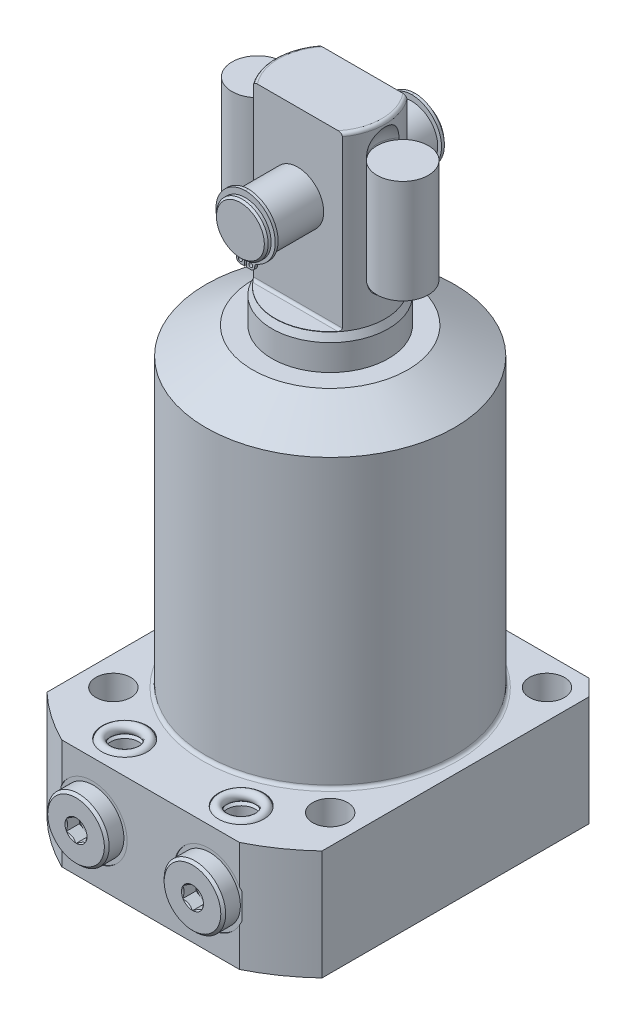
SolidWorks part; units mm, degrees
material "AISI 1020"
ref_plane "Front Plane" through (0, 0, 0) normal (0, 0, 1) x (1, 0, 0)
ref_plane "Top Plane" through (0, 0, 0) normal (0, 1, 0) x (1, 0, 0)
ref_plane "Right Plane" through (0, 0, 0) normal (1, 0, 0) x (0, 0, -1)
sketch "Sketch1" plane through (0, 0, 0) normal (0, 0, 1) x (1, 0, 0)
  line L0 (18, 0) -> (18, 105)
  line L1 (18, 105) -> (17, 107.1445)
  line L2 (17, 107.1445) -> (17, 159.25)
  line L3 (16, 160.25) -> (0, 160.25)
  line L4 (0, 61.9815) -> (0, 93.5758) construction
  line L8 (0, -3.075) -> (0, 64.575) construction
  line L9 (18, 0) -> (0, 0)
  line L10 (0, 0) -> (0, 160.25)
  line L11 (-25.0821, -34) -> (21.8096, -34) construction
  arc A0 (17, 159.25) -> (16, 160.25) centre (16, 159.25) ccw
  dimension "D1" = 1
  dimension "D2" = 36
  dimension "D3" = 34
  dimension "D4" = 55.25
  dimension "D5" = 34
  dimension "D6" = 25
  dimension "D7" = 194.25
revolve "PLUNGER" add sketch "Sketch1" angle 360 about L8
ref_plane "FLAT_SKTCH_PLN" through (0, 0, 0) normal (1, 0, 0) x (0, 0, -1)
sketch "Sketch17" plane through (0, 0, 0) normal (1, 0, 0) x (0, 0, -1)
  line L0 (16, 160.25) -> (-16, 160.25) construction
  line L1 (17, 107.1445) -> (17, 159.25) construction
  line L2 (16, 160.25) -> (-16, 160.25)
  line L3 (17, 107.1445) -> (17, 159.25)
  line L5 (10, 160.25) -> (17, 160.25)
  line L6 (10, 160.25) -> (10, 108.05)
  line L7 (10.8, 107.25) -> (17, 107.25)
  line L8 (17, 160.25) -> (17, 107.25)
  line L9 (0, 159.25) -> (0, 107.1445) construction
  line L10 (0, 57.0947) -> (0, 92.2162) construction
  line L11 (0, 105) -> (0, 0) construction
  line L12 (0, 105) -> (0, 107.1445) construction
  line L13 (-17, 160.25) -> (-17, 107.25)
  line L14 (-10.8, 107.25) -> (-17, 107.25)
  line L15 (-10, 160.25) -> (-10, 108.05)
  line L16 (-10, 160.25) -> (-17, 160.25)
  line L17 (-17, 107.1445) -> (-17, 159.25)
  arc A0 (10, 108.05) -> (10.8, 107.25) centre (10.8, 108.05) ccw
  arc A1 (-10, 108.05) -> (-10.8, 107.25) centre (-10.8, 108.05) cw
  dimension "D3" = 0.8
  dimension "D1" = 53
  dimension "D2" = 20
extrude "FLATS" cut sketch "Sketch17" against normal mid plane 100 contours L6 A0 L7 L8 L5 | L13 L14 A1 L15 L16
sketch "Sketch22" plane through (0, 0, 0) normal (1, 0, 0) x (0, 0, -1)
  line L0 (-11.5689, 136.25) -> (12.3381, 136.25) construction
  line L1 (0, 87.9433) -> (0, 65.5754) construction
  line L2 (0, 163.8601) -> (0, 151.5297) construction
  line L3 (0, 159.25) -> (0, 107.1445) construction
  line L4 (10, 160.25) -> (-10, 160.25) construction
  line L5 (10, 160.25) -> (-10, 160.25)
  line L6 (27.75, 143.65) -> (27.15, 144.25)
  line L7 (27.15, 144.25) -> (26.25, 144.25)
  line L8 (27.75, 143.65) -> (27.75, 136.25)
  line L9 (27.75, 136.25) -> (-27.75, 136.25)
  line L11 (26.25, 144.25) -> (26.25, 143.7175)
  line L12 (26.25, 143.7175) -> (25.25, 143.7175)
  line L13 (25.25, 143.7175) -> (25.25, 144.25)
  line L14 (25.25, 144.25) -> (-25.25, 144.25)
  line L15 (-25.25, 143.7175) -> (-25.25, 144.25)
  line L16 (-26.25, 143.7175) -> (-25.25, 143.7175)
  line L17 (-26.25, 144.25) -> (-26.25, 143.7175)
  line L18 (-27.75, 143.65) -> (-27.75, 136.25)
  line L19 (-27.15, 144.25) -> (-26.25, 144.25)
  line L20 (-27.75, 143.65) -> (-27.15, 144.25)
  dimension "D1" = 24
  dimension "D2" = 45
  dimension "D3" = 0.6
  dimension "D4" = 16
  dimension "D5" = 1
  dimension "D6" = 14.935
  dimension "D7" = 55.5
  dimension "D8" = 50.5
revolve "PIVOT_PIN" add sketch "Sketch22" angle 360 about L0
sketch "Sketch23" plane through (0, 0, -25.25) normal (0, 0, -1) x (-1, 0, 0)
  line L0 (0, 79.466) -> (0, 70.8639) construction
  line L1 (0, 159.25) -> (0, 107.1445) construction
  line L2 (0, 136.25) -> (-4.1358, 126.8979) construction
  line L3 (-0.35, 125.7079) -> (-1.61, 125.7079)
  line L4 (0, 136.25) -> (4.1358, 126.8979) construction
  line L5 (0.35, 128.5079) -> (0.35, 125.7079)
  line L6 (-0.35, 128.5079) -> (-0.35, 125.7079)
  line L7 (0.35, 125.7079) -> (1.61, 125.7079)
  arc A0 (0.35, 128.5079) -> (-0.35, 128.5079) centre (0, 136.25) ccw
  arc A1 (-2.8, 126.8979) -> (-1.61, 125.7079) centre (-1.61, 126.8979) ccw
  arc A2 (-2.8, 126.8979) -> (-3.5955, 128.1195) centre (-4.1358, 126.8979) ccw
  arc A3 (-3.5955, 128.1195) -> (0, 146.03) centre (0.1884, 136.676) cw
  circle A4 centre (-1.61, 126.8979) radius 0.595
  circle A5 centre (1.61, 126.8979) radius 0.595
  arc A6 (3.5955, 128.1195) -> (0, 146.03) centre (-0.1884, 136.676) ccw
  arc A7 (2.8, 126.8979) -> (3.5955, 128.1195) centre (4.1358, 126.8979) cw
  arc A8 (2.8, 126.8979) -> (1.61, 125.7079) centre (1.61, 126.8979) cw
  point P17 (-3.1344, 129.1621)
  point P27 (3.1344, 129.1621)
  point P28 (0, 144)
  dimension "D1" = 15.5
  dimension "D3" = 1.19
  dimension "D8" = 1.19
  dimension "D2" = 0.7
  dimension "D4" = 2.8
  dimension "D5" = 2.8
  dimension "D6" = 2.03
  dimension "D7" = 1.14
extrude "RETAINING_RING" add sketch "Sketch23" along normal blind 0.89
ref_plane "PIN_CL" through (0, 0, 0) normal (0, 0, 1) x (1, 0, 0)
mirror "RETAINING_RING-OPP" about plane through (0, 0, 0) normal (0, 0, 1) of "RETAINING_RING"
sketch "Sketch20" plane through (0, 0, 0) normal (0, 0, 1) x (1, 0, 0)
  line L0 (-12.49, 160.25) -> (12.49, 160.25) construction
  line L1 (-12.49, 160.25) -> (12.49, 160.25)
  line L2 (0, 87.5232) -> (0, 65.9324) construction
  line L3 (0, 163.858) -> (0, 151.534) construction
  line L4 (0, 159.25) -> (0, 107.1445) construction
  line L5 (22.4375, 82.048) -> (22.4375, 54.8595) construction
  line L6 (14.5, 152.75) -> (14.5, 119.75)
  line L7 (22.4375, 160.6875) -> (22.4375, 111.8125)
  arc A0 (22.4375, 160.6875) -> (14.5, 152.75) centre (22.4375, 152.75) ccw
  arc A1 (14.5, 119.75) -> (22.4375, 111.8125) centre (22.4375, 119.75) ccw
  dimension "D3" = 33
  dimension "D1" = 14.5
  dimension "D2" = 15.875
  dimension "D4" = 7.5
revolve "SPRING_SLOT" cut sketch "Sketch20" angle 360 about L5
mirror "SPRING_SLOT_OPP" about plane through (0, 0, 0) normal (1, 0, 0) of "SPRING_SLOT"
sketch "Sketch24" plane through (0, 0, 0) normal (0, 0, 1) x (1, 0, 0)
  line L0 (7.2759, 136.25) -> (-10.8708, 136.25) construction
  line L1 (-22.4075, 84.5678) -> (-22.4075, 68.6953) construction
  line L2 (-14.5, 119.75) -> (-14.5, 152.75) construction
  line L3 (-14.47, 152.25) -> (-22.4075, 152.25)
  line L4 (-14.47, 152.25) -> (-14.47, 120.25)
  line L6 (-22.4075, 152.25) -> (-22.4075, 120.25)
  line L7 (-14.47, 120.25) -> (-22.4075, 120.25)
  dimension "D1" = 15.875
  dimension "D2" = 32
  dimension "D3" = 0.03
revolve "SPRING" add sketch "Sketch24" angle 360 about L1
mirror "SPRING_OPP" about plane through (0, 0, 0) normal (1, 0, 0) of "SPRING"
sketch "Sketch6" plane through (0, 0, 0) normal (0, 0, 1) x (1, 0, 0)
  line L0 (0, -34) -> (0, 67.6291) construction
  line L1 (0, 97) -> (24, 97)
  line L2 (24, 97) -> (38.385, 88.6948)
  line L3 (61.915, 0) -> (61.915, -34)
  line L4 (0, -34) -> (61.915, -34)
  line L5 (38.385, 0) -> (38.385, 88.6948)
  line L6 (61.915, 0) -> (38.385, 0)
  line L7 (0, -34) -> (0, 97)
  dimension "D1" = 76.77
  dimension "D2" = 34
  dimension "D3" = 131
  dimension "D4" = 123.83
  dimension "D5" = 30
  dimension "D6" = 48
revolve "BODY_REVOLVE" add sketch "Sketch6" angle 360 about L0
sketch "Sketch7" plane through (0, 0, 0) normal (0, 1, 0) x (-1, 0, 0)
  line L0 (0, 0) -> (0, -52.3237) construction
  line L1 (-42.5, 55.5) -> (42.5, 55.5)
  line L2 (-42.5, 55.5) -> (-42.5, -42.5)
  line L3 (-42.5, -42.5) -> (42.5, -42.5)
  line L4 (42.5, 55.5) -> (42.5, -42.5)
  dimension "D1" = 85
  dimension "D2" = 98
  dimension "D3" = 42.5
extrude "FLANGE_SIDES" cut sketch "Sketch7" against normal through all flip side to cut
sketch "Sketch8" plane through (0, -34, 0) normal (0, -1, 0) x (1, 0, 0)
  circle A0 centre (-33.5, 33.5) radius 5.4
  dimension "D1" = 10.8
  dimension "D2" = 33.5
  dimension "D3" = 33.5
extrude "MOUNTING HOLES" cut sketch "Sketch8" against normal through all
pattern_circular "MOUNTING_PATTERN" count 4 over 360 about axis through (0, 0, 0) along (0, 1, 0) of "MOUNTING HOLES"
chamfer "FLANGE_CHAMFER" distance 5 angle 45 2 edges at (-42.5, -17, -42.5) (42.5, -17, -42.5)
fillet "BODY_FILLET" radius 1 1 edges at (38.385, 0, 0)
ref_plane "FLANGE-PORT_PLANE" through (0, -17, 0) normal (0, -1, 0) x (1, 0, 0)
sketch "Sketch11" plane through (0, -17, 0) normal (0, -1, 0) x (1, 0, 0)
  line L0 (-18, 42.9716) -> (-18, 19.7499) construction
  line L1 (-28.75, 55.5) -> (-28.75, 55.25)
  line L3 (-28.75, 55.25) -> (-24.65, 55.25)
  line L4 (-24.65, 55.25) -> (-23.945, 54.545)
  line L5 (-23.945, 54.545) -> (-23.945, 36.53)
  line L6 (-23.945, 36.53) -> (-18, 36.53)
  line L7 (-18, 36.53) -> (-18, 55.5)
  line L8 (-18, 55.5) -> (-28.75, 55.5)
  line L10 (27.4448, 55.5) -> (-27.4448, 55.5) construction
  dimension "D1" = 18
  dimension "D2" = 0.25
  dimension "D3" = 11.89
  dimension "D4" = 18.72
  dimension "D5" = 21.5
  dimension "D6" = 45
  dimension "D7" = 0.705
revolve "PORT SPOT FACE" cut sketch "Sketch11" angle 360 about L0
ref_plane "MANIFOLD_PORT_PLANE" through (0, 0, 45.5) normal (0, 0, 1) x (1, 0, 0)
sketch "Sketch13" plane through (0, 0, 45.5) normal (0, 0, 1) x (1, 0, 0)
  line L0 (-22.375, -22) -> (-22.375, -31)
  line L1 (-22.375, -31) -> (-23.125, -31.75)
  line L2 (-23.125, -31.75) -> (-25, -31.75)
  line L3 (-25, -31.75) -> (-25, -34)
  line L5 (-25, -34) -> (-18, -34)
  line L6 (-18, -34) -> (-18, -22)
  line L7 (-18, -22) -> (-22.375, -22)
  line L8 (-18, 15.2099) -> (-18, -4.3918) construction
  line L10 (27.4448, -34) -> (-27.4448, -34) construction
  dimension "D1" = 18
  dimension "D2" = 8.75
  dimension "D3" = 12
  dimension "D4" = 2.25
  dimension "D5" = 14
  dimension "D6" = 45
  dimension "D7" = 0.75
revolve "BOTTOM_MANIFOLD_PORT" cut sketch "Sketch13" angle 360 about L8
sketch "Sketch14" plane through (0, -17, 0) normal (0, -1, 0) x (1, 0, 0)
  line L0 (-18, 32.5881) -> (-18, 43.5576) construction
  line L1 (-18, 36.53) -> (-18, 54.545) construction
  line L2 (-21.4, 60.55) -> (-26.75, 60.55)
  line L3 (-26.75, 60.55) -> (-27.5, 59.8)
  line L4 (-27.5, 59.8) -> (-27.5, 55.25)
  line L5 (-7.25, 55.25) -> (-27.9447, 55.25) construction
  line L6 (-27.5, 55.25) -> (-22.125, 55.25)
  line L7 (-11.35, 55.25) -> (-24.65, 55.25) construction
  line L8 (-22.125, 55.25) -> (-22.125, 52.7472)
  line L9 (-22.125, 52.7472) -> (-18, 52.7472)
  line L10 (-18, 52.7472) -> (-18, 52.7482)
  line L11 (-18, 52.7482) -> (-21, 54.5508)
  line L12 (-21, 54.5508) -> (-21, 60.15)
  line L13 (-21, 60.15) -> (-21.4, 60.55)
  dimension "D1" = 8.25
  dimension "D2" = 2.5028
  dimension "D3" = 59
  dimension "D4" = 6
  dimension "D5" = 5.3
  dimension "D6" = 19
  dimension "D7" = 45
  dimension "D8" = 0.75
  dimension "D9" = 45
  dimension "D10" = 0.4
  dimension "D11" = 0.001
revolve "BSPP_PLUGHEAD" add sketch "Sketch14" angle 360 about L0
sketch "Sketch15" plane through (0, 0, 60.55) normal (0, 0, 1) x (1, 0, 0)
  line L1 (-15, -18.7321) -> (-15, -15.2679)
  line L2 (-15, -15.2679) -> (-18, -13.5359)
  line L3 (-18, -13.5359) -> (-21, -15.2679)
  line L4 (-21, -15.2679) -> (-21, -18.7321)
  line L5 (-21, -18.7321) -> (-18, -20.4641)
  line L6 (-18, -20.4641) -> (-15, -18.7321)
  circle A0 centre (-18, -17) radius 3 construction
  dimension "D1" = 6
extrude "BSPP_PLUG_HEX" cut sketch "Sketch15" against normal blind 4.06
mirror "MANIFOLD_TOP_MIRROR" about plane through (0, -17, 0) normal (0, -1, 0) of "BOTTOM_MANIFOLD_PORT"
mirror "BSPP-MANIFOLD_MIRROR" about plane through (0, 0, 0) normal (1, 0, 0) of "MANIFOLD_TOP_MIRROR", "PORT SPOT FACE", "BOTTOM_MANIFOLD_PORT", "BSPP_PLUGHEAD", "BSPP_PLUG_HEX"
sketch "Sketch16" plane through (0, 0, 45.5) normal (0, 0, 1) x (1, 0, 0)
  line L1 (-18, 9.3219) -> (-18, -15.1063) construction
  line L2 (-18, -31) -> (-18, -22) construction
  line L3 (27.4448, -34) -> (-27.4448, -34) construction
  circle A0 centre (-23.5, -33.25) radius 1.5
  dimension "D1" = 3
  dimension "D3" = 0.75
  dimension "D2" = 11
revolve "MANIFOLD_O-RING" add sketch "Sketch16" angle 360 about L1
mirror "MANIFOLD_O-RING_MIRROR" about plane through (0, 0, 0) normal (1, 0, 0) of bodies 128
mirror "MANIFOLD_O-RING_MIRROR_TOP" about plane through (0, -17, 0) normal (0, -1, 0) of bodies 128 130
